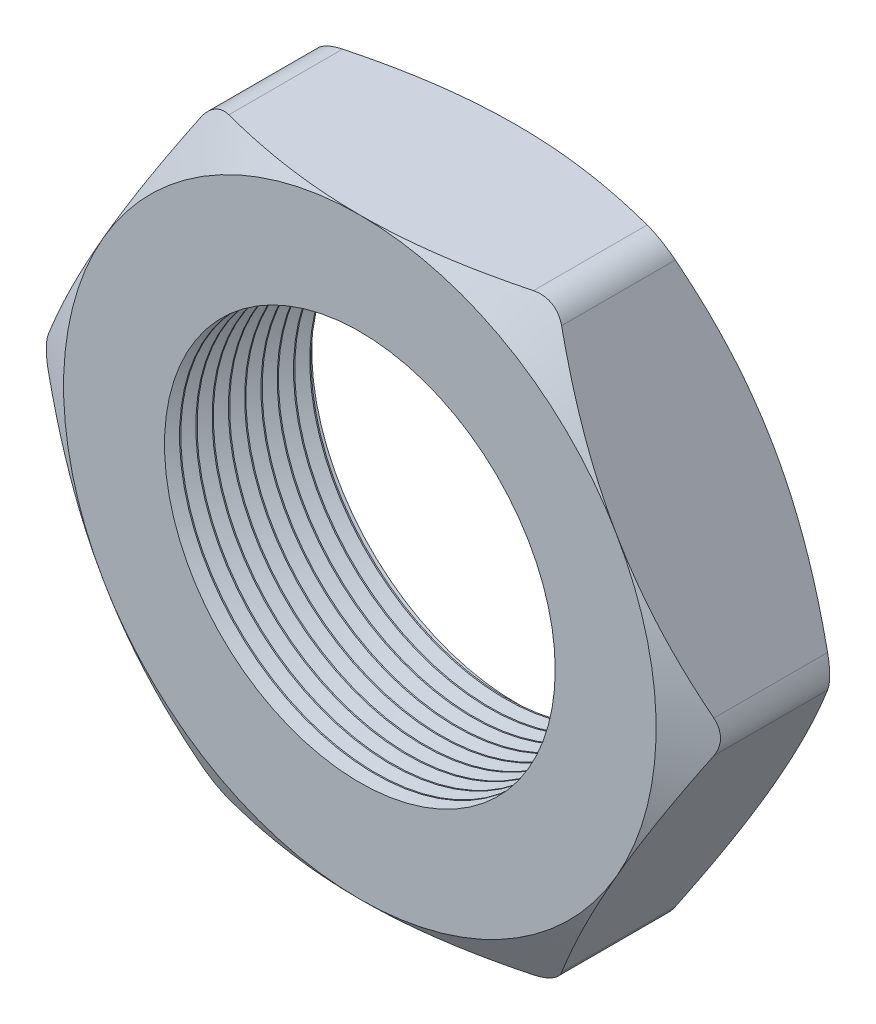
SolidWorks part; units mm, degrees
ref_plane "Front Plane" through (0, 0, 0) normal (0, 0, 1) x (1, 0, 0)
ref_plane "Top Plane" through (0, 0, 0) normal (0, 1, 0) x (1, 0, 0)
ref_plane "Right Plane" through (0, 0, 0) normal (1, 0, 0) x (0, 0, -1)
sketch "Sketch1" plane through (0, 0, 0) normal (0, 0, 1) x (1, 0, 0)
  line L1 (-13.3449, 0) -> (-6.6724, -11.557)
  line L2 (-6.6724, -11.557) -> (6.6724, -11.557)
  line L3 (6.6724, -11.557) -> (13.3449, 0)
  line L4 (13.3449, 0) -> (6.6724, 11.557)
  line L5 (6.6724, 11.557) -> (-6.6724, 11.557)
  line L6 (-6.6724, 11.557) -> (-13.3449, 0)
  circle A0 centre (0, 0) radius 11.557 construction
  circle A1 centre (0, 0) radius 7.62
  dimension "TS" = 15.24
  dimension "H" = 23.114
extrude "Extrude1" add sketch "Sketch1" along normal blind 6.096
sketch "Sketch2" plane through (0, 0, 6.096) normal (0, 0, 1) x (1, 0, 0)
  line L0 (6.6724, 11.557) -> (-6.6724, 11.557) construction
  circle A0 centre (0, 0) radius 11.557
extrude "Cut-Extrude1" cut sketch "Sketch2" against normal through all draft 60 flip side to cut
sketch "Sketch3" plane through (0, 0, 0) normal (0, 0, -1) x (-1, 0, 0)
  line L0 (-6.6724, 11.557) -> (6.6724, 11.557) construction
  circle A0 centre (0, 0) radius 11.557
extrude "Cut-Extrude2" cut sketch "Sketch3" against normal through all draft 60 flip side to cut
fillet "Fillet1" radius 1.27 6 edges at (13.3449, 0, 3.048) (6.6724, -11.557, 3.048) (-6.6724, -11.557, 3.048) (-13.3449, 0, 3.048) (-6.6724, 11.557, 3.048) (6.6724, 11.557, 3.048)
sketch "Sketch4" plane through (0, 0, 0) normal (0, 1, 0) x (1, 0, 0)
  line L0 (-7.62, -6.096) -> (-7.62, -5.5094)
  line L1 (-7.62, 0) -> (-7.62, -6.096) construction
  line L2 (-7.62, -5.5094) -> (-8.128, -5.8027)
  line L3 (-8.128, -5.8027) -> (-7.62, -6.096)
  dimension "D1" = 60
  dimension "D2" = 60
  dimension "D3" = 0.508
revolve "Cut-Revolve1" cut sketch "Sketch4" angle 360 about axis through (0, 0, 0) along (0, 0, 1)
pattern_linear "LPattern1" count 10 spacing 0.635 along (0, 0, -1) of "Cut-Revolve1"
